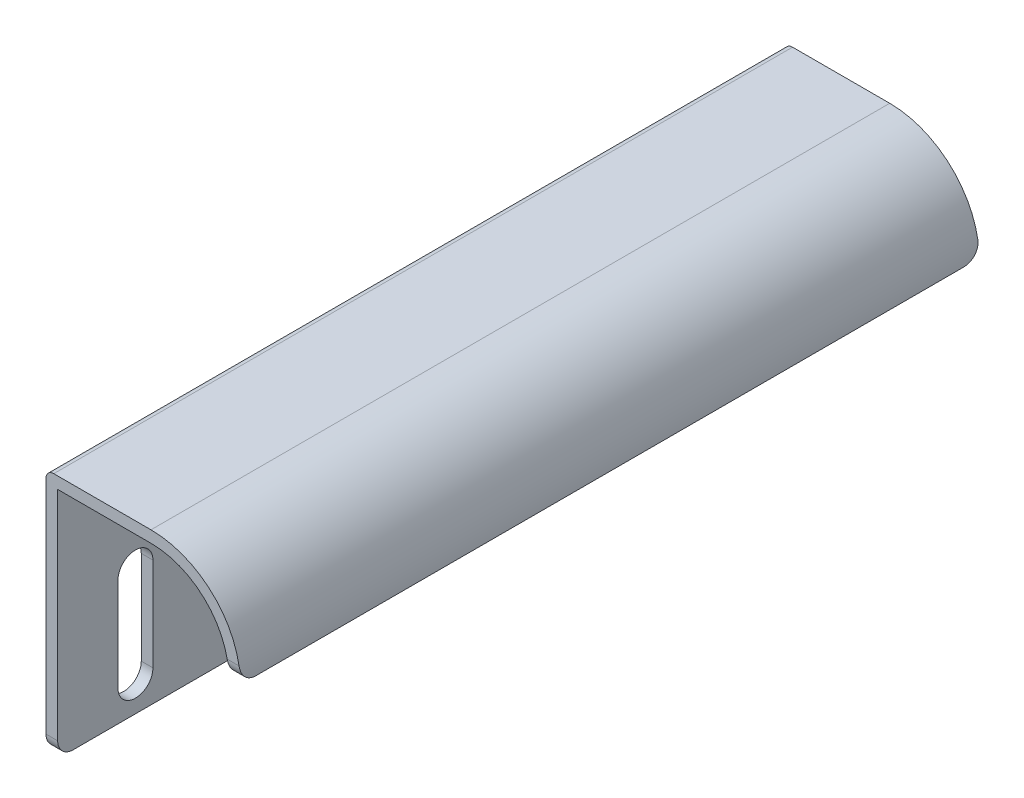
SolidWorks part; units mm, degrees
ref_plane "Front Plane" through (0, 0, 0) normal (0, 0, 1) x (1, 0, 0)
ref_plane "Top Plane" through (0, 0, 0) normal (0, 1, 0) x (1, 0, 0)
ref_plane "Right Plane" through (0, 0, 0) normal (1, 0, 0) x (0, 0, -1)
sketch "Sketch1" plane through (0, 0, 0) normal (0, 0, 1) x (1, 0, 0)
  line L0 (-9.7634, -19.4163) -> (-9.7634, 12.0837)
  line L1 (-9.7634, 12.0837) -> (3.7366, 12.0837)
  line L2 (13.7366, 0.5837) -> (15.2366, 0.5837)
  line L3 (3.7366, 10.5837) -> (-8.2634, 10.5837)
  line L4 (-8.2634, 10.5837) -> (-8.2634, -19.4163)
  line L5 (-8.2634, -19.4163) -> (-9.7634, -19.4163)
  arc A0 (15.2366, 0.5837) -> (3.7366, 12.0837) centre (3.7366, 0.5837) ccw
  arc A1 (13.7366, 0.5837) -> (3.7366, 10.5837) centre (3.7366, 0.5837) ccw
  dimension "D3" = 23
  dimension "D4" = 20
  dimension "D1" = 13.5
  dimension "D2" = 31.5
  dimension "D5" = 1.5
extrude "Boss-Extrude1" add sketch "Sketch1" along normal blind 95
fillet "Fillet1" radius 1 1 edges at (-9.7634, 12.0837, 47.5)
fillet "Fillet2" radius 2 4 edges at (-9.0134, -19.4163, 0) (-9.0134, -19.4163, 95) (14.4866, 0.5837, 0) (14.4866, 0.5837, 95)
sketch "Sketch2" plane through (-8.2634, 0, 0) normal (1, 0, 0) x (0, 0, -1)
  line L2 (-87.25, -3.4163) -> (-87.25, -15.4163)
  line L4 (-82.75, -3.4163) -> (-82.75, -15.4163)
  line L6 (-12.25, -3.4163) -> (-12.25, -15.4163)
  line L8 (-7.75, -3.4163) -> (-7.75, -15.4163)
  arc A0 (-82.75, -3.4163) -> (-87.25, -3.4163) centre (-85, -3.4163) ccw
  arc A1 (-87.25, -15.4163) -> (-82.75, -15.4163) centre (-85, -15.4163) ccw
  arc A2 (-7.75, -3.4163) -> (-12.25, -3.4163) centre (-10, -3.4163) ccw
  arc A3 (-12.25, -15.4163) -> (-7.75, -15.4163) centre (-10, -15.4163) ccw
  dimension "D1" = 4.5
  dimension "D2" = 4.5
  dimension "D3" = 12
  dimension "D4" = 12
extrude "Cut-Extrude1" cut sketch "Sketch2" against normal through all
